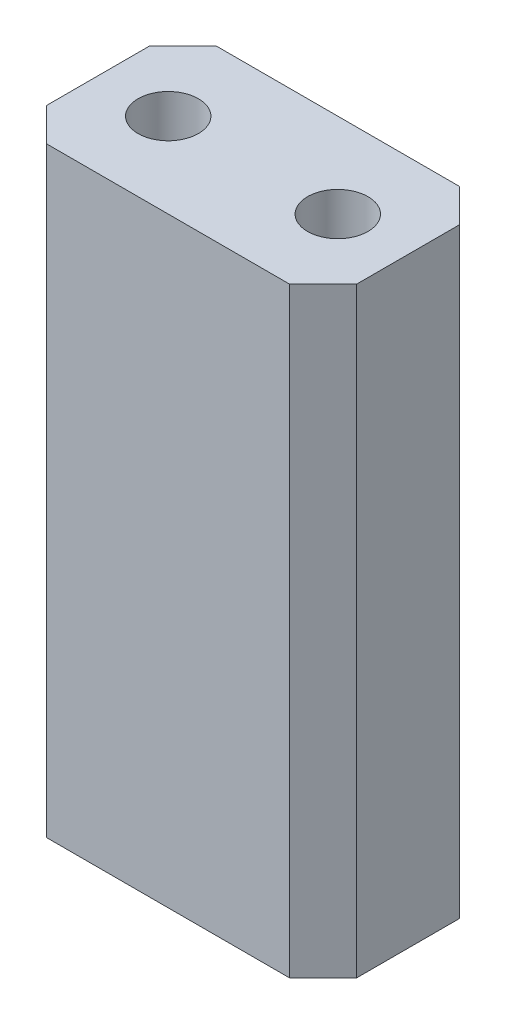
SolidWorks part; units mm, degrees
ref_plane "Спереди" through (0, 0, 0) normal (0, 0, 1) x (1, 0, 0)
ref_plane "Сверху" through (0, 0, 0) normal (0, 1, 0) x (1, 0, 0)
ref_plane "Справа" through (0, 0, 0) normal (1, 0, 0) x (0, 0, -1)
sketch "Эскиз1" plane through (0, 0, 0) normal (0, 1, 0) x (1, 0, 0)
  line L0 (-2.32, 0) -> (2.32, 0) construction
  line L1 (-2.32, -1.27) -> (2.32, -1.27)
  line L3 (-2.32, 1.27) -> (2.32, 1.27)
  line L4 (2.32, -1.27) -> (2.32, 1.27)
  line L5 (-2.32, -1.27) -> (2.32, 1.27) construction
  line L6 (-2.32, 1.27) -> (2.32, -1.27) construction
  line L12 (-1.59, -0.32) -> (-0.95, -0.32)
  line L17 (-1.59, -0.32) -> (-1.59, 0.32)
  line L18 (-1.59, 0.32) -> (-0.95, 0.32)
  line L19 (-0.95, -0.32) -> (-0.95, 0.32)
  line L20 (-1.59, -0.32) -> (-0.95, 0.32) construction
  line L21 (-1.59, 0.32) -> (-0.95, -0.32) construction
  line L22 (0.95, -0.32) -> (1.59, -0.32)
  line L23 (0.95, -0.32) -> (0.95, 0.32)
  line L24 (0.95, 0.32) -> (1.59, 0.32)
  line L25 (1.59, -0.32) -> (1.59, 0.32)
  line L26 (0.95, -0.32) -> (1.59, 0.32) construction
  line L27 (0.95, 0.32) -> (1.59, -0.32) construction
  line L28 (-2.32, 1.27) -> (-2.32, -1.27)
  point P0 (0, 0)
  point P7 (1.27, 0)
  point P8 (-1.27, 0)
  dimension "D1" = 4.64
  dimension "D2" = 2.54
  dimension "D3" = 0.64
  dimension "D4" = 0.64
  dimension "D5" = 0.95
  dimension "D6" = 1.9
  dimension "D7" = 0.64
  dimension "D8" = 0.64
extrude "Бобышка-Вытянуть1" add sketch "Эскиз1" along normal blind 6
sketch "Эскиз2" plane through (0, 6, 0) normal (0, 1, 0) x (1, 0, 0)
  line L0 (-2.32, 0) -> (2.32, 0) construction
  line L1 (-2.32, 1.27) -> (-2.32, -1.27) construction
  line L2 (2.32, -1.27) -> (2.32, 1.27) construction
  line L4 (-2.32, -1.27) -> (2.32, -1.27)
  line L5 (-2.32, -1.27) -> (-2.32, 1.27)
  line L6 (-2.32, 1.27) -> (2.32, 1.27)
  line L7 (2.32, -1.27) -> (2.32, 1.27)
  line L8 (-2.32, -1.27) -> (2.32, 1.27) construction
  line L9 (-2.32, 1.27) -> (2.32, -1.27) construction
  circle A0 centre (-1.27, 0) radius 0.4525
  circle A1 centre (1.27, 0) radius 0.4525
  point P6 (0, 0)
extrude "Бобышка-Вытянуть2" add sketch "Эскиз2" along normal blind 3
chamfer "Фаска1" distance 0.5 angle 45 4 edges at (-2.32, 4.5, -1.27) (-2.32, 4.5, 1.27) (2.32, 4.5, -1.27) (2.32, 4.5, 1.27)
